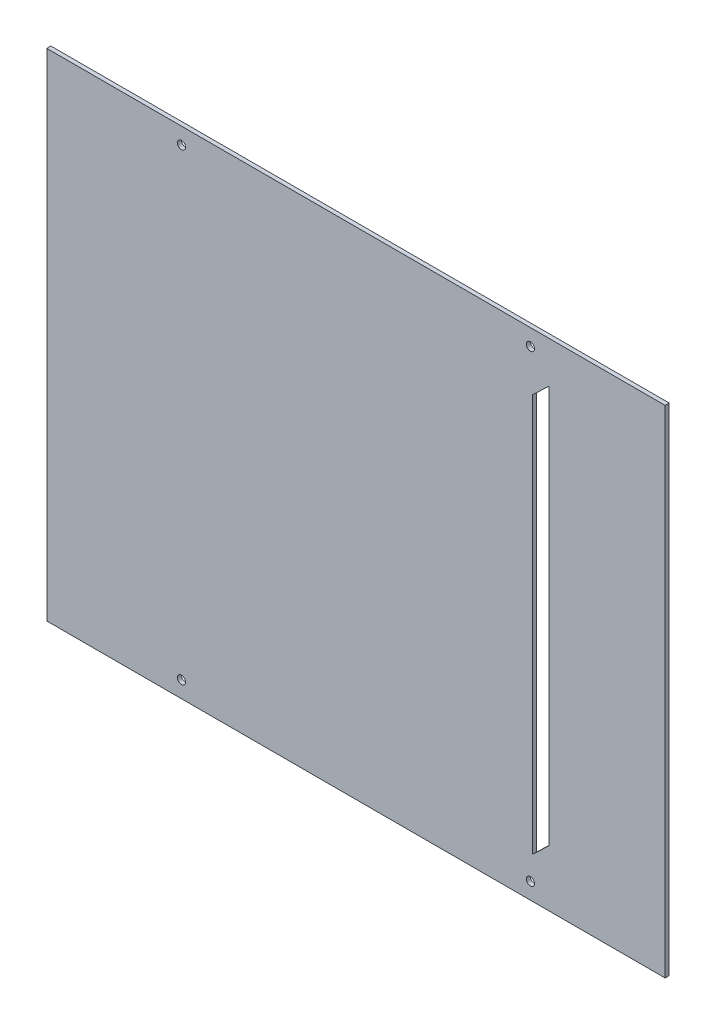
SolidWorks part; units mm, degrees
ref_plane "Front Plane" through (0, 0, 0) normal (0, 0, 1) x (1, 0, 0)
ref_plane "Top Plane" through (0, 0, 0) normal (0, 1, 0) x (1, 0, 0)
ref_plane "Right Plane" through (0, 0, 0) normal (1, 0, 0) x (0, 0, -1)
sketch "Sketch1" plane through (0, 0, 0) normal (0, 0, 1) x (1, 0, 0)
  line L0 (0, 0) -> (-206.9982, 0) construction
  line L1 (151.5, -121.5) -> (-151.5, -121.5)
  line L2 (151.5, -121.5) -> (151.5, 121.5)
  line L3 (151.5, 121.5) -> (-151.5, 121.5)
  line L4 (-151.5, -121.5) -> (-151.5, 121.5)
  line L5 (151.5, -121.5) -> (-151.5, 121.5) construction
  line L6 (151.5, 121.5) -> (-151.5, -121.5) construction
  line L7 (141.5, -113.4802) -> (-141.5, -113.4802) construction
  line L8 (141.5, -113.4802) -> (141.5, 113.4802) construction
  line L9 (141.5, 113.4802) -> (-141.5, 113.4802) construction
  line L10 (-141.5, -113.4802) -> (-141.5, 113.4802) construction
  line L11 (141.5, -113.4802) -> (-141.5, 113.4802) construction
  line L12 (141.5, 113.4802) -> (-141.5, -113.4802) construction
  line L13 (86.5, 93.5) -> (86.5, -96.5)
  line L14 (86.5, 93.5) -> (94.5, 101.0781)
  line L15 (94.5, -93.9219) -> (94.5, 93.5)
  line L16 (94.5, 101.0781) -> (94.5, 93.5)
  line L17 (94.5, -93.9219) -> (86.5, -101.5)
  line L18 (86.5, -101.5) -> (86.5, -96.5)
  line L19 (86.5, -96.5) -> (87.1166, -96.1701)
  circle A0 centre (-85.5, 113.4802) radius 2
  circle A1 centre (85.5, 113.4802) radius 2
  circle A2 centre (85.5, -113.4802) radius 2
  circle A3 centre (-85.5, -113.4802) radius 2
  point P0 (0, 0)
  point P5 (0, 0)
  dimension "D4" = 4
  dimension "D5" = 4
  dimension "D1" = 303
  dimension "D2" = 243
  dimension "D3" = 10
  dimension "D6" = 66
  dimension "D7" = 66
  dimension "D8" = 57
  dimension "D9" = 8
  dimension "D10" = 202.5781
  dimension "D11" = 20
extrude "Boss-Extrude1" add sketch "Sketch1" along normal blind 2 contours L4 L1 L2 L3 A2 A1 A0 L17 L18 L13 L14 L16 L15 A3
